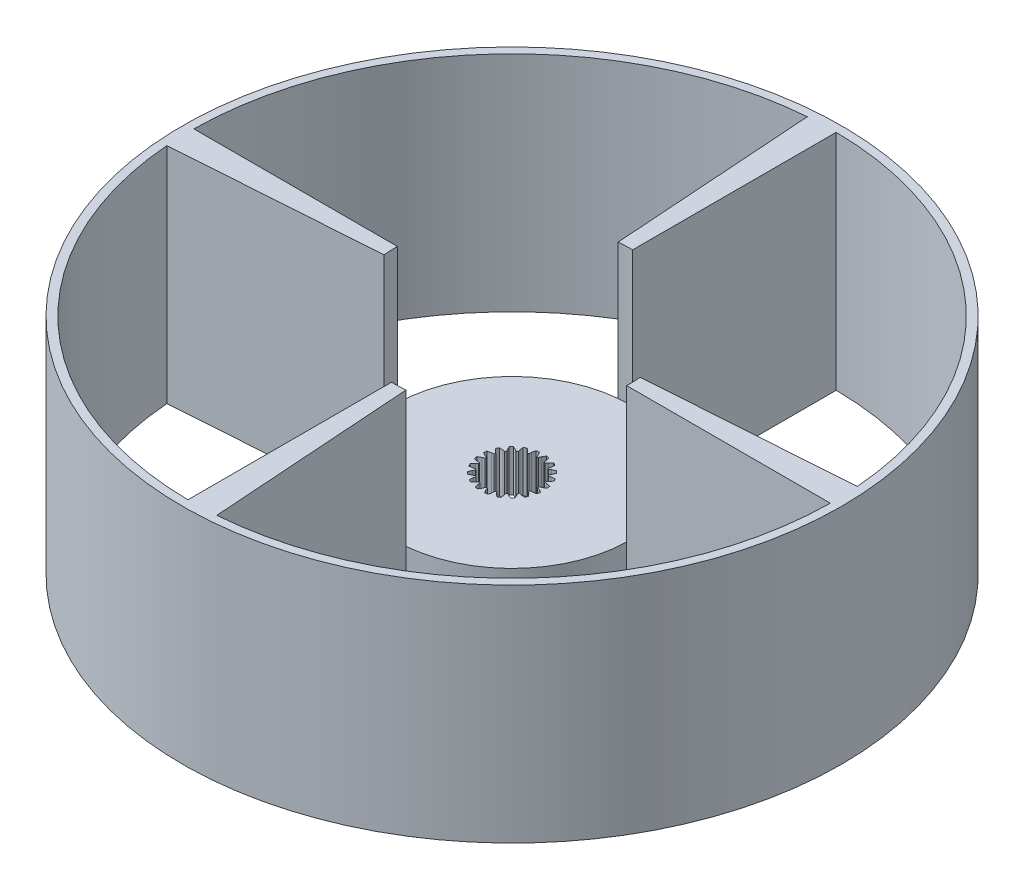
SolidWorks part; units mm, degrees
ref_plane "Ön Düzlem" through (0, 0, 0) normal (0, 0, 1) x (1, 0, 0)
ref_plane "Üst Düzlem" through (0, 0, 0) normal (0, 1, 0) x (1, 0, 0)
ref_plane "Sağ Düzlem" through (0, 0, 0) normal (1, 0, 0) x (0, 0, -1)
sketch "Çizim1" plane through (0, 0, 0) normal (0, 1, 0) x (1, 0, 0)
  circle A0 centre (0, 0) radius 115
  circle A5 centre (0, 0) radius 5
  dimension "D1" = 230
extrude "Ekstrüzyon-İnce1" add sketch "Çizim1" along normal blind 80 thin contours A0
ref_plane "Düzlem1" through (0, 16.5, 0) normal (0, -1, 0) x (-1, 0, 0)
sketch "Çizim4" plane through (0, 16.5, 0) normal (0, -1, 0) x (-1, 0, 0)
  line L0 (-1.4135, -11.2112) -> (-0.7173, -10.0847)
  line L1 (-0.7173, -10.0847) -> (-0.4138, -9.2908)
  line L2 (0.1143, -9.2993) -> (0.3921, -10.1026)
  line L3 (0.3921, -10.1026) -> (1.0516, -11.251)
  line L4 (2.1201, -11.0993) -> (2.4341, -9.8128)
  line L5 (2.4341, -9.8128) -> (2.4775, -8.9639)
  line L6 (2.9823, -8.8088) -> (3.4948, -9.487)
  line L7 (3.4948, -9.487) -> (4.4769, -10.3753)
  line L8 (5.4463, -9.9009) -> (5.3473, -8.5804)
  line L9 (5.3473, -8.5804) -> (5.1262, -7.7596)
  line L10 (5.5585, -7.4561) -> (6.2554, -7.9427)
  line L11 (6.2554, -7.9427) -> (7.4639, -8.4841)
  line L12 (8.2392, -7.7334) -> (7.7371, -6.508)
  line L13 (7.7371, -6.508) -> (7.2732, -5.7958)
  line L14 (7.5905, -5.3735) -> (8.4037, -5.6209)
  line L15 (8.4037, -5.6209) -> (9.7203, -5.7624)
  line L16 (10.2257, -4.8088) -> (9.3695, -3.7986)
  line L17 (9.3695, -3.7986) -> (8.7082, -3.2646)
  line L18 (8.8795, -2.7649) -> (9.7293, -2.749)
  line L19 (9.7293, -2.749) -> (11.0253, -2.4766)
  line L20 (11.2112, -1.4135) -> (10.0847, -0.7173)
  line L21 (10.0847, -0.7173) -> (9.2908, -0.4138)
  line L22 (9.2993, 0.1143) -> (10.1026, 0.3921)
  line L23 (10.1026, 0.3921) -> (11.251, 1.0516)
  line L24 (11.0993, 2.1201) -> (9.8128, 2.4341)
  line L25 (9.8128, 2.4341) -> (8.9639, 2.4775)
  line L26 (8.8088, 2.9823) -> (9.487, 3.4948)
  line L27 (9.487, 3.4948) -> (10.3753, 4.4769)
  line L28 (9.9009, 5.4463) -> (8.5804, 5.3473)
  line L29 (8.5804, 5.3473) -> (7.7596, 5.1262)
  line L30 (7.4561, 5.5585) -> (7.9427, 6.2554)
  line L31 (7.9427, 6.2554) -> (8.4841, 7.4639)
  line L32 (7.7334, 8.2392) -> (6.508, 7.7371)
  line L33 (6.508, 7.7371) -> (5.7958, 7.2732)
  line L34 (5.3735, 7.5905) -> (5.6209, 8.4037)
  line L35 (5.6209, 8.4037) -> (5.7624, 9.7203)
  line L36 (4.8088, 10.2257) -> (3.7986, 9.3695)
  line L37 (3.7986, 9.3695) -> (3.2646, 8.7082)
  line L38 (2.7649, 8.8795) -> (2.749, 9.7293)
  line L39 (2.749, 9.7293) -> (2.4766, 11.0253)
  line L40 (1.4135, 11.2112) -> (0.7173, 10.0847)
  line L41 (0.7173, 10.0847) -> (0.4138, 9.2908)
  line L42 (-0.1143, 9.2993) -> (-0.3921, 10.1026)
  line L43 (-0.3921, 10.1026) -> (-1.0516, 11.251)
  line L44 (-2.1201, 11.0993) -> (-2.4341, 9.8128)
  line L45 (-2.4341, 9.8128) -> (-2.4775, 8.9639)
  line L46 (-2.9823, 8.8088) -> (-3.4948, 9.487)
  line L47 (-3.4948, 9.487) -> (-4.4769, 10.3753)
  line L48 (-5.4463, 9.9009) -> (-5.3473, 8.5804)
  line L49 (-5.3473, 8.5804) -> (-5.1262, 7.7596)
  line L50 (-5.5585, 7.4561) -> (-6.2554, 7.9427)
  line L51 (-6.2554, 7.9427) -> (-7.4639, 8.4841)
  line L52 (-8.2392, 7.7334) -> (-7.7371, 6.508)
  line L53 (-7.7371, 6.508) -> (-7.2732, 5.7958)
  line L54 (-7.5905, 5.3735) -> (-8.4037, 5.6209)
  line L55 (-8.4037, 5.6209) -> (-9.7203, 5.7624)
  line L56 (-10.2257, 4.8088) -> (-9.3695, 3.7986)
  line L57 (-9.3695, 3.7986) -> (-8.7082, 3.2646)
  line L58 (-8.8795, 2.7649) -> (-9.7293, 2.749)
  line L59 (-9.7293, 2.749) -> (-11.0253, 2.4766)
  line L60 (-11.2112, 1.4135) -> (-10.0847, 0.7173)
  line L61 (-10.0847, 0.7173) -> (-9.2908, 0.4138)
  line L62 (-9.2993, -0.1143) -> (-10.1026, -0.3921)
  line L63 (-10.1026, -0.3921) -> (-11.251, -1.0516)
  line L64 (-11.0993, -2.1201) -> (-9.8128, -2.4341)
  line L65 (-9.8128, -2.4341) -> (-8.9639, -2.4775)
  line L66 (-8.8088, -2.9823) -> (-9.487, -3.4948)
  line L67 (-9.487, -3.4948) -> (-10.3753, -4.4769)
  line L68 (-9.9009, -5.4463) -> (-8.5804, -5.3473)
  line L69 (-8.5804, -5.3473) -> (-7.7596, -5.1262)
  line L70 (-7.4561, -5.5585) -> (-7.9427, -6.2554)
  line L71 (-7.9427, -6.2554) -> (-8.4841, -7.4639)
  line L72 (-7.7334, -8.2392) -> (-6.508, -7.7371)
  line L73 (-6.508, -7.7371) -> (-5.7958, -7.2732)
  line L74 (-5.3735, -7.5905) -> (-5.6209, -8.4037)
  line L75 (-5.6209, -8.4037) -> (-5.7624, -9.7203)
  line L76 (-4.8088, -10.2257) -> (-3.7986, -9.3695)
  line L77 (-3.7986, -9.3695) -> (-3.2646, -8.7082)
  line L78 (-2.7649, -8.8795) -> (-2.749, -9.7293)
  line L79 (-2.749, -9.7293) -> (-2.4766, -11.0253)
  line L80 (-1.5664, -10.8879) -> (-0.9874, -9.9511)
  line L81 (-2.4495, -9.6953) -> (-2.223, -10.773)
  line L82 (-2.4691, -8.6547) -> (-2.4495, -9.6953)
  line L83 (-4.0142, -9.1589) -> (-3.3602, -8.3492)
  line L84 (-4.8542, -9.871) -> (-4.0142, -9.1589)
  line L85 (-5.3257, -8.4639) -> (-5.4433, -9.5588)
  line L86 (-5.0227, -7.4681) -> (-5.3257, -8.4639)
  line L87 (-6.648, -7.4702) -> (-5.7758, -6.9022)
  line L88 (-7.667, -7.8878) -> (-6.648, -7.4702)
  line L89 (-7.6805, -6.4039) -> (-8.1307, -7.4089)
  line L90 (-7.0846, -5.5505) -> (-7.6805, -6.4039)
  line L91 (-8.631, -5.0503) -> (-7.626, -4.7795)
  line L92 (-9.7292, -5.1325) -> (-8.631, -5.0503)
  line L93 (-9.2835, -3.7171) -> (-10.0222, -4.5337)
  line L94 (-8.4531, -3.0895) -> (-9.2835, -3.7171)
  line L95 (-9.7692, -2.136) -> (-8.7297, -2.189)
  line L96 (-10.839, -1.8749) -> (-9.7692, -2.136)
  line L97 (-9.9778, -0.6664) -> (-10.9327, -1.2148)
  line L98 (-8.9941, -0.3262) -> (-9.9778, -0.6664)
  line L99 (-9.9511, 0.9874) -> (-8.9789, 0.6157)
  line L100 (-10.8879, 1.5664) -> (-9.9511, 0.9874)
  line L101 (-9.6953, 2.4495) -> (-10.773, 2.223)
  line L102 (-8.6547, 2.4691) -> (-9.6953, 2.4495)
  line L103 (-9.1589, 4.0142) -> (-8.3492, 3.3602)
  line L104 (-9.871, 4.8542) -> (-9.1589, 4.0142)
  line L105 (-8.4639, 5.3257) -> (-9.5588, 5.4433)
  line L106 (-7.4681, 5.0227) -> (-8.4639, 5.3257)
  line L107 (-7.4702, 6.648) -> (-6.9022, 5.7758)
  line L108 (-7.8878, 7.667) -> (-7.4702, 6.648)
  line L109 (-6.4039, 7.6805) -> (-7.4089, 8.1307)
  line L110 (-5.5505, 7.0846) -> (-6.4039, 7.6805)
  line L111 (-5.0503, 8.631) -> (-4.7795, 7.626)
  line L112 (-5.1325, 9.7292) -> (-5.0503, 8.631)
  line L113 (-3.7171, 9.2835) -> (-4.5337, 10.0222)
  line L114 (-3.0895, 8.4531) -> (-3.7171, 9.2835)
  line L115 (-2.136, 9.7692) -> (-2.189, 8.7297)
  line L116 (-1.8749, 10.839) -> (-2.136, 9.7692)
  line L117 (-0.6664, 9.9778) -> (-1.2148, 10.9327)
  line L118 (-0.3262, 8.9941) -> (-0.6664, 9.9778)
  line L119 (0.9874, 9.9511) -> (0.6157, 8.9789)
  line L120 (1.5664, 10.8879) -> (0.9874, 9.9511)
  line L121 (2.4495, 9.6953) -> (2.223, 10.773)
  line L122 (2.4691, 8.6547) -> (2.4495, 9.6953)
  line L123 (4.0142, 9.1589) -> (3.3602, 8.3492)
  line L124 (4.8542, 9.871) -> (4.0142, 9.1589)
  line L125 (5.3257, 8.4639) -> (5.4433, 9.5588)
  line L126 (5.0227, 7.4681) -> (5.3257, 8.4639)
  line L127 (6.648, 7.4702) -> (5.7758, 6.9022)
  line L128 (7.667, 7.8878) -> (6.648, 7.4702)
  line L129 (7.6805, 6.4039) -> (8.1307, 7.4089)
  line L130 (7.0846, 5.5505) -> (7.6805, 6.4039)
  line L131 (8.631, 5.0503) -> (7.626, 4.7795)
  line L132 (9.7292, 5.1325) -> (8.631, 5.0503)
  line L133 (9.2835, 3.7171) -> (10.0222, 4.5337)
  line L134 (8.4531, 3.0895) -> (9.2835, 3.7171)
  line L135 (9.7692, 2.136) -> (8.7297, 2.189)
  line L136 (10.839, 1.8749) -> (9.7692, 2.136)
  line L137 (9.9778, 0.6664) -> (10.9327, 1.2148)
  line L138 (8.9941, 0.3262) -> (9.9778, 0.6664)
  line L139 (9.9511, -0.9874) -> (8.9789, -0.6157)
  line L140 (10.8879, -1.5664) -> (9.9511, -0.9874)
  line L141 (9.6953, -2.4495) -> (10.773, -2.223)
  line L142 (8.6547, -2.4691) -> (9.6953, -2.4495)
  line L143 (9.1589, -4.0142) -> (8.3492, -3.3602)
  line L144 (9.871, -4.8542) -> (9.1589, -4.0142)
  line L145 (8.4639, -5.3257) -> (9.5588, -5.4433)
  line L146 (7.4681, -5.0227) -> (8.4639, -5.3257)
  line L147 (7.4702, -6.648) -> (6.9022, -5.7758)
  line L148 (7.8878, -7.667) -> (7.4702, -6.648)
  line L149 (6.4039, -7.6805) -> (7.4089, -8.1307)
  line L150 (5.5505, -7.0846) -> (6.4039, -7.6805)
  line L151 (5.0503, -8.631) -> (4.7795, -7.626)
  line L152 (5.1325, -9.7292) -> (5.0503, -8.631)
  line L153 (3.7171, -9.2835) -> (4.5337, -10.0222)
  line L154 (3.0895, -8.4531) -> (3.7171, -9.2835)
  line L155 (2.136, -9.7692) -> (2.189, -8.7297)
  line L156 (1.8749, -10.839) -> (2.136, -9.7692)
  line L157 (0.6664, -9.9778) -> (1.2148, -10.9327)
  line L158 (0.3262, -8.9941) -> (0.6664, -9.9778)
  line L159 (-0.9874, -9.9511) -> (-0.6157, -8.9789)
  line L160 (-1.5664, -10.8879) -> (-0.9874, -9.9511)
  line L161 (-2.4495, -9.6953) -> (-2.223, -10.773)
  line L162 (-2.4691, -8.6547) -> (-2.4495, -9.6953)
  line L163 (-4.0142, -9.1589) -> (-3.3602, -8.3492)
  line L164 (-4.8542, -9.871) -> (-4.0142, -9.1589)
  line L165 (-5.3257, -8.4639) -> (-5.4433, -9.5588)
  line L166 (-5.0227, -7.4681) -> (-5.3257, -8.4639)
  line L167 (-6.648, -7.4702) -> (-5.7758, -6.9022)
  line L168 (-7.667, -7.8878) -> (-6.648, -7.4702)
  line L169 (-7.6805, -6.4039) -> (-8.1307, -7.4089)
  line L170 (-7.0846, -5.5505) -> (-7.6805, -6.4039)
  line L171 (-8.631, -5.0503) -> (-7.626, -4.7795)
  line L172 (-9.7292, -5.1325) -> (-8.631, -5.0503)
  line L173 (-9.2835, -3.7171) -> (-10.0222, -4.5337)
  line L174 (-8.4531, -3.0895) -> (-9.2835, -3.7171)
  line L175 (-9.7692, -2.136) -> (-8.7297, -2.189)
  line L176 (-10.839, -1.8749) -> (-9.7692, -2.136)
  line L177 (-9.9778, -0.6664) -> (-10.9327, -1.2148)
  line L178 (-8.9941, -0.3262) -> (-9.9778, -0.6664)
  line L179 (-9.9511, 0.9874) -> (-8.9789, 0.6157)
  line L180 (-10.8879, 1.5664) -> (-9.9511, 0.9874)
  line L181 (-9.6953, 2.4495) -> (-10.773, 2.223)
  line L182 (-8.6547, 2.4691) -> (-9.6953, 2.4495)
  line L183 (-9.1589, 4.0142) -> (-8.3492, 3.3602)
  line L184 (-9.871, 4.8542) -> (-9.1589, 4.0142)
  line L185 (-8.4639, 5.3257) -> (-9.5588, 5.4433)
  line L186 (-7.4681, 5.0227) -> (-8.4639, 5.3257)
  line L187 (-7.4702, 6.648) -> (-6.9022, 5.7758)
  line L188 (-7.8878, 7.667) -> (-7.4702, 6.648)
  line L189 (-6.4039, 7.6805) -> (-7.4089, 8.1307)
  line L190 (-5.5505, 7.0846) -> (-6.4039, 7.6805)
  line L191 (-5.0503, 8.631) -> (-4.7795, 7.626)
  line L192 (-5.1325, 9.7292) -> (-5.0503, 8.631)
  line L193 (-3.7171, 9.2835) -> (-4.5337, 10.0222)
  line L194 (-3.0895, 8.4531) -> (-3.7171, 9.2835)
  line L195 (-2.136, 9.7692) -> (-2.189, 8.7297)
  line L196 (-1.8749, 10.839) -> (-2.136, 9.7692)
  line L197 (-0.6664, 9.9778) -> (-1.2148, 10.9327)
  line L198 (-0.3262, 8.9941) -> (-0.6664, 9.9778)
  line L199 (0.9874, 9.9511) -> (0.6157, 8.9789)
  line L200 (1.5664, 10.8879) -> (0.9874, 9.9511)
  line L201 (2.4495, 9.6953) -> (2.223, 10.773)
  line L202 (2.4691, 8.6547) -> (2.4495, 9.6953)
  line L203 (4.0142, 9.1589) -> (3.3602, 8.3492)
  line L204 (4.8542, 9.871) -> (4.0142, 9.1589)
  line L205 (5.3257, 8.4639) -> (5.4433, 9.5588)
  line L206 (5.0227, 7.4681) -> (5.3257, 8.4639)
  line L207 (6.648, 7.4702) -> (5.7758, 6.9022)
  line L208 (7.667, 7.8878) -> (6.648, 7.4702)
  line L209 (7.6805, 6.4039) -> (8.1307, 7.4089)
  line L210 (7.0846, 5.5505) -> (7.6805, 6.4039)
  line L211 (8.631, 5.0503) -> (7.626, 4.7795)
  line L212 (9.7292, 5.1325) -> (8.631, 5.0503)
  line L213 (9.2835, 3.7171) -> (10.0222, 4.5337)
  line L214 (8.4531, 3.0895) -> (9.2835, 3.7171)
  line L215 (9.7692, 2.136) -> (8.7297, 2.189)
  line L216 (10.839, 1.8749) -> (9.7692, 2.136)
  line L217 (9.9778, 0.6664) -> (10.9327, 1.2148)
  line L218 (8.9941, 0.3262) -> (9.9778, 0.6664)
  line L219 (9.9511, -0.9874) -> (8.9789, -0.6157)
  line L220 (10.8879, -1.5664) -> (9.9511, -0.9874)
  line L221 (9.6953, -2.4495) -> (10.773, -2.223)
  line L222 (8.6547, -2.4691) -> (9.6953, -2.4495)
  line L223 (9.1589, -4.0142) -> (8.3492, -3.3602)
  line L224 (9.871, -4.8542) -> (9.1589, -4.0142)
  line L225 (8.4639, -5.3257) -> (9.5588, -5.4433)
  line L226 (7.4681, -5.0227) -> (8.4639, -5.3257)
  line L227 (7.4702, -6.648) -> (6.9022, -5.7758)
  line L228 (7.8878, -7.667) -> (7.4702, -6.648)
  line L229 (6.4039, -7.6805) -> (7.4089, -8.1307)
  line L230 (5.5505, -7.0846) -> (6.4039, -7.6805)
  line L231 (5.0503, -8.631) -> (4.7795, -7.626)
  line L232 (5.1325, -9.7292) -> (5.0503, -8.631)
  line L233 (3.7171, -9.2835) -> (4.5337, -10.0222)
  line L234 (3.0895, -8.4531) -> (3.7171, -9.2835)
  line L235 (2.136, -9.7692) -> (2.189, -8.7297)
  line L236 (1.8749, -10.839) -> (2.136, -9.7692)
  line L237 (0.6664, -9.9778) -> (1.2148, -10.9327)
  line L238 (0.3262, -8.9941) -> (0.6664, -9.9778)
  line L239 (-0.9874, -9.9511) -> (-0.6157, -8.9789)
  circle A0 centre (0, 0) radius 42.0972
  arc A3 (-0.4138, -9.2908) -> (0.1143, -9.2993) centre (0, 0) ccw
  arc A4 (1.0516, -11.251) -> (2.1201, -11.0993) centre (0, 0) ccw
  arc A5 (2.4775, -8.9639) -> (2.9823, -8.8088) centre (0, 0) ccw
  arc A6 (4.4769, -10.3753) -> (5.4463, -9.9009) centre (0, 0) ccw
  arc A7 (5.1262, -7.7596) -> (5.5585, -7.4561) centre (0, 0) ccw
  arc A8 (7.4639, -8.4841) -> (8.2392, -7.7334) centre (0, 0) ccw
  arc A9 (7.2732, -5.7958) -> (7.5905, -5.3735) centre (0, 0) ccw
  arc A10 (9.7203, -5.7624) -> (10.2257, -4.8088) centre (0, 0) ccw
  arc A11 (8.7082, -3.2646) -> (8.8795, -2.7649) centre (0, 0) ccw
  arc A12 (11.0253, -2.4766) -> (11.2112, -1.4135) centre (0, 0) ccw
  arc A13 (9.2908, -0.4138) -> (9.2993, 0.1143) centre (0, 0) ccw
  arc A14 (11.251, 1.0516) -> (11.0993, 2.1201) centre (0, 0) ccw
  arc A15 (8.9639, 2.4775) -> (8.8088, 2.9823) centre (0, 0) ccw
  arc A16 (10.3753, 4.4769) -> (9.9009, 5.4463) centre (0, 0) ccw
  arc A17 (7.7596, 5.1262) -> (7.4561, 5.5585) centre (0, 0) ccw
  arc A18 (8.4841, 7.4639) -> (7.7334, 8.2392) centre (0, 0) ccw
  arc A19 (5.7958, 7.2732) -> (5.3735, 7.5905) centre (0, 0) ccw
  arc A20 (5.7624, 9.7203) -> (4.8088, 10.2257) centre (0, 0) ccw
  arc A21 (3.2646, 8.7082) -> (2.7649, 8.8795) centre (0, 0) ccw
  arc A22 (2.4766, 11.0253) -> (1.4135, 11.2112) centre (0, 0) ccw
  arc A23 (0.4138, 9.2908) -> (-0.1143, 9.2993) centre (0, 0) ccw
  arc A24 (-1.0516, 11.251) -> (-2.1201, 11.0993) centre (0, 0) ccw
  arc A25 (-2.4775, 8.9639) -> (-2.9823, 8.8088) centre (0, 0) ccw
  arc A26 (-4.4769, 10.3753) -> (-5.4463, 9.9009) centre (0, 0) ccw
  arc A27 (-5.1262, 7.7596) -> (-5.5585, 7.4561) centre (0, 0) ccw
  arc A28 (-7.4639, 8.4841) -> (-8.2392, 7.7334) centre (0, 0) ccw
  arc A29 (-7.2732, 5.7958) -> (-7.5905, 5.3735) centre (0, 0) ccw
  arc A30 (-9.7203, 5.7624) -> (-10.2257, 4.8088) centre (0, 0) ccw
  arc A31 (-8.7082, 3.2646) -> (-8.8795, 2.7649) centre (0, 0) ccw
  arc A32 (-11.0253, 2.4766) -> (-11.2112, 1.4135) centre (0, 0) ccw
  arc A33 (-9.2908, 0.4138) -> (-9.2993, -0.1143) centre (0, 0) ccw
  arc A34 (-11.251, -1.0516) -> (-11.0993, -2.1201) centre (0, 0) ccw
  arc A35 (-8.9639, -2.4775) -> (-8.8088, -2.9823) centre (0, 0) ccw
  arc A36 (-10.3753, -4.4769) -> (-9.9009, -5.4463) centre (0, 0) ccw
  arc A37 (-7.7596, -5.1262) -> (-7.4561, -5.5585) centre (0, 0) ccw
  arc A38 (-8.4841, -7.4639) -> (-7.7334, -8.2392) centre (0, 0) ccw
  arc A39 (-5.7958, -7.2732) -> (-5.3735, -7.5905) centre (0, 0) ccw
  arc A40 (-5.7624, -9.7203) -> (-4.8088, -10.2257) centre (0, 0) ccw
  arc A41 (-3.2646, -8.7082) -> (-2.7649, -8.8795) centre (0, 0) ccw
  arc A42 (-2.4766, -11.0253) -> (-1.4135, -11.2112) centre (0, 0) ccw
  arc A43 (-2.223, -10.773) -> (-1.5664, -10.8879) centre (0, 0) ccw
  arc A44 (-3.3602, -8.3492) -> (-2.4691, -8.6547) centre (0, 0) ccw
  arc A45 (-5.4433, -9.5588) -> (-4.8542, -9.871) centre (0, 0) ccw
  arc A46 (-5.7758, -6.9022) -> (-5.0227, -7.4681) centre (0, 0) ccw
  arc A47 (-8.1307, -7.4089) -> (-7.667, -7.8878) centre (0, 0) ccw
  arc A48 (-7.626, -4.7795) -> (-7.0846, -5.5505) centre (0, 0) ccw
  arc A49 (-10.0222, -4.5337) -> (-9.7292, -5.1325) centre (0, 0) ccw
  arc A50 (-8.7297, -2.189) -> (-8.4531, -3.0895) centre (0, 0) ccw
  arc A51 (-10.9327, -1.2148) -> (-10.839, -1.8749) centre (0, 0) ccw
  arc A52 (-8.9789, 0.6157) -> (-8.9941, -0.3262) centre (0, 0) ccw
  arc A53 (-10.773, 2.223) -> (-10.8879, 1.5664) centre (0, 0) ccw
  arc A54 (-8.3492, 3.3602) -> (-8.6547, 2.4691) centre (0, 0) ccw
  arc A55 (-9.5588, 5.4433) -> (-9.871, 4.8542) centre (0, 0) ccw
  arc A56 (-6.9022, 5.7758) -> (-7.4681, 5.0227) centre (0, 0) ccw
  arc A57 (-7.4089, 8.1307) -> (-7.8878, 7.667) centre (0, 0) ccw
  arc A58 (-4.7795, 7.626) -> (-5.5505, 7.0846) centre (0, 0) ccw
  arc A59 (-4.5337, 10.0222) -> (-5.1325, 9.7292) centre (0, 0) ccw
  arc A60 (-2.189, 8.7297) -> (-3.0895, 8.4531) centre (0, 0) ccw
  arc A61 (-1.2148, 10.9327) -> (-1.8749, 10.839) centre (0, 0) ccw
  arc A62 (0.6157, 8.9789) -> (-0.3262, 8.9941) centre (0, 0) ccw
  arc A63 (2.223, 10.773) -> (1.5664, 10.8879) centre (0, 0) ccw
  arc A64 (3.3602, 8.3492) -> (2.4691, 8.6547) centre (0, 0) ccw
  arc A65 (5.4433, 9.5588) -> (4.8542, 9.871) centre (0, 0) ccw
  arc A66 (5.7758, 6.9022) -> (5.0227, 7.4681) centre (0, 0) ccw
  arc A67 (8.1307, 7.4089) -> (7.667, 7.8878) centre (0, 0) ccw
  arc A68 (7.626, 4.7795) -> (7.0846, 5.5505) centre (0, 0) ccw
  arc A69 (10.0222, 4.5337) -> (9.7292, 5.1325) centre (0, 0) ccw
  arc A70 (8.7297, 2.189) -> (8.4531, 3.0895) centre (0, 0) ccw
  arc A71 (10.9327, 1.2148) -> (10.839, 1.8749) centre (0, 0) ccw
  arc A72 (8.9789, -0.6157) -> (8.9941, 0.3262) centre (0, 0) ccw
  arc A73 (10.773, -2.223) -> (10.8879, -1.5664) centre (0, 0) ccw
  arc A74 (8.3492, -3.3602) -> (8.6547, -2.4691) centre (0, 0) ccw
  arc A75 (9.5588, -5.4433) -> (9.871, -4.8542) centre (0, 0) ccw
  arc A76 (6.9022, -5.7758) -> (7.4681, -5.0227) centre (0, 0) ccw
  arc A77 (7.4089, -8.1307) -> (7.8878, -7.667) centre (0, 0) ccw
  arc A78 (4.7795, -7.626) -> (5.5505, -7.0846) centre (0, 0) ccw
  arc A79 (4.5337, -10.0222) -> (5.1325, -9.7292) centre (0, 0) ccw
  arc A80 (2.189, -8.7297) -> (3.0895, -8.4531) centre (0, 0) ccw
  arc A81 (1.2148, -10.9327) -> (1.8749, -10.839) centre (0, 0) ccw
  arc A82 (-0.6157, -8.9789) -> (0.3262, -8.9941) centre (0, 0) ccw
  arc A83 (-2.223, -10.773) -> (-1.5664, -10.8879) centre (0, 0) ccw
  arc A84 (-3.3602, -8.3492) -> (-2.4691, -8.6547) centre (0, 0) ccw
  arc A85 (-5.4433, -9.5588) -> (-4.8542, -9.871) centre (0, 0) ccw
  arc A86 (-5.7758, -6.9022) -> (-5.0227, -7.4681) centre (0, 0) ccw
  arc A87 (-8.1307, -7.4089) -> (-7.667, -7.8878) centre (0, 0) ccw
  arc A88 (-7.626, -4.7795) -> (-7.0846, -5.5505) centre (0, 0) ccw
  arc A89 (-10.0222, -4.5337) -> (-9.7292, -5.1325) centre (0, 0) ccw
  arc A90 (-8.7297, -2.189) -> (-8.4531, -3.0895) centre (0, 0) ccw
  arc A91 (-10.9327, -1.2148) -> (-10.839, -1.8749) centre (0, 0) ccw
  arc A92 (-8.9789, 0.6157) -> (-8.9941, -0.3262) centre (0, 0) ccw
  arc A93 (-10.773, 2.223) -> (-10.8879, 1.5664) centre (0, 0) ccw
  arc A94 (-8.3492, 3.3602) -> (-8.6547, 2.4691) centre (0, 0) ccw
  arc A95 (-9.5588, 5.4433) -> (-9.871, 4.8542) centre (0, 0) ccw
  arc A96 (-6.9022, 5.7758) -> (-7.4681, 5.0227) centre (0, 0) ccw
  arc A97 (-7.4089, 8.1307) -> (-7.8878, 7.667) centre (0, 0) ccw
  arc A98 (-4.7795, 7.626) -> (-5.5505, 7.0846) centre (0, 0) ccw
  arc A99 (-4.5337, 10.0222) -> (-5.1325, 9.7292) centre (0, 0) ccw
  arc A100 (-2.189, 8.7297) -> (-3.0895, 8.4531) centre (0, 0) ccw
  arc A101 (-1.2148, 10.9327) -> (-1.8749, 10.839) centre (0, 0) ccw
  arc A102 (0.6157, 8.9789) -> (-0.3262, 8.9941) centre (0, 0) ccw
  arc A103 (2.223, 10.773) -> (1.5664, 10.8879) centre (0, 0) ccw
  arc A104 (3.3602, 8.3492) -> (2.4691, 8.6547) centre (0, 0) ccw
  arc A105 (5.4433, 9.5588) -> (4.8542, 9.871) centre (0, 0) ccw
  arc A106 (5.7758, 6.9022) -> (5.0227, 7.4681) centre (0, 0) ccw
  arc A107 (8.1307, 7.4089) -> (7.667, 7.8878) centre (0, 0) ccw
  arc A108 (7.626, 4.7795) -> (7.0846, 5.5505) centre (0, 0) ccw
  arc A109 (10.0222, 4.5337) -> (9.7292, 5.1325) centre (0, 0) ccw
  arc A110 (8.7297, 2.189) -> (8.4531, 3.0895) centre (0, 0) ccw
  arc A111 (10.9327, 1.2148) -> (10.839, 1.8749) centre (0, 0) ccw
  arc A112 (8.9789, -0.6157) -> (8.9941, 0.3262) centre (0, 0) ccw
  arc A113 (10.773, -2.223) -> (10.8879, -1.5664) centre (0, 0) ccw
  arc A114 (8.3492, -3.3602) -> (8.6547, -2.4691) centre (0, 0) ccw
  arc A115 (9.5588, -5.4433) -> (9.871, -4.8542) centre (0, 0) ccw
  arc A116 (6.9022, -5.7758) -> (7.4681, -5.0227) centre (0, 0) ccw
  arc A117 (7.4089, -8.1307) -> (7.8878, -7.667) centre (0, 0) ccw
  arc A118 (4.7795, -7.626) -> (5.5505, -7.0846) centre (0, 0) ccw
  arc A119 (4.5337, -10.0222) -> (5.1325, -9.7292) centre (0, 0) ccw
  arc A120 (2.189, -8.7297) -> (3.0895, -8.4531) centre (0, 0) ccw
  arc A121 (1.2148, -10.9327) -> (1.8749, -10.839) centre (0, 0) ccw
  arc A122 (-0.6157, -8.9789) -> (0.3262, -8.9941) centre (0, 0) ccw
  dimension "D1" = 0
  dimension "D2" = 0.3
extrude "Yükseklik-Ekstrüzyon4" add sketch "Çizim4" along normal up to surface (15 mm away) contours A0 A42 L79 L78 A41 L77 L76 A40 L75 L74 A39 L73 L72 A38 L71 L70 A37 L69 L68 A36 L67 L66 A35 L65 L64 A34 L63 L62 A33 L61 L60 A32 L59 L58 A31 L57 L56 A30 L55 L54 A29 L53 L52 A28 L51 L50 A27 L49 L48 A26
sketch "Çizim5" plane through (0, 80, 0) normal (0, 1, 0) x (1, 0, 0)
  line L0 (41.9122, 3.9417) -> (114.6518, 8.9417)
  line L1 (42.0839, -1.0583) -> (114.9951, -1.0583)
  line L2 (3.9417, -41.9122) -> (8.9417, -114.6518)
  line L3 (-1.0583, -42.0839) -> (-1.0583, -114.9951)
  line L4 (-41.9122, -3.9417) -> (-114.6518, -8.9417)
  line L5 (-42.0839, 1.0583) -> (-114.9951, 1.0583)
  line L6 (-3.9417, 41.9122) -> (-8.9417, 114.6518)
  line L7 (1.0583, 42.0839) -> (1.0583, 114.9951)
  circle A0 centre (0, 0) radius 42.0972 construction
  circle A1 centre (0, 0) radius 115 construction
  circle A2 centre (0, 0) radius 42.0972
  circle A3 centre (0, 0) radius 115
  point P23 (0, 0)
  circle M4 centre (0, 0) radius 115
  dimension "D1" = 10
  dimension "D2" = 5
  dimension "D3" = 4
extrude "Yükseklik-Ekstrüzyon5" add sketch "Çizim5" against normal up to surface (80 mm away) contours A2 L5 L4 M4 | A2 L3 L2 M4 | A2 L1 L0 M4 | A2 L7 L6 M4 up to face at (118, 0, 0)
sketch "Çizim6" plane through (0, 0, 0) normal (0, -1, 0) x (1, 0, 0)
  line L3 (-42.0839, -1.0583) -> (41.9122, -3.9417)
  line L4 (-41.9122, 3.9417) -> (42.0839, 1.0583)
  arc A2 (41.9122, -3.9417) -> (42.0839, 1.0583) centre (0, 0) ccw construction
  arc A3 (-41.9122, 3.9417) -> (-42.0839, -1.0583) centre (0, 0) ccw construction
  arc A4 (41.9122, -3.9417) -> (42.0839, 1.0583) centre (0, 0) ccw
  arc A5 (-41.9122, 3.9417) -> (-42.0839, -1.0583) centre (0, 0) ccw
extrude "Yükseklik-Ekstrüzyon11" add sketch "Çizim6" against normal blind 3
